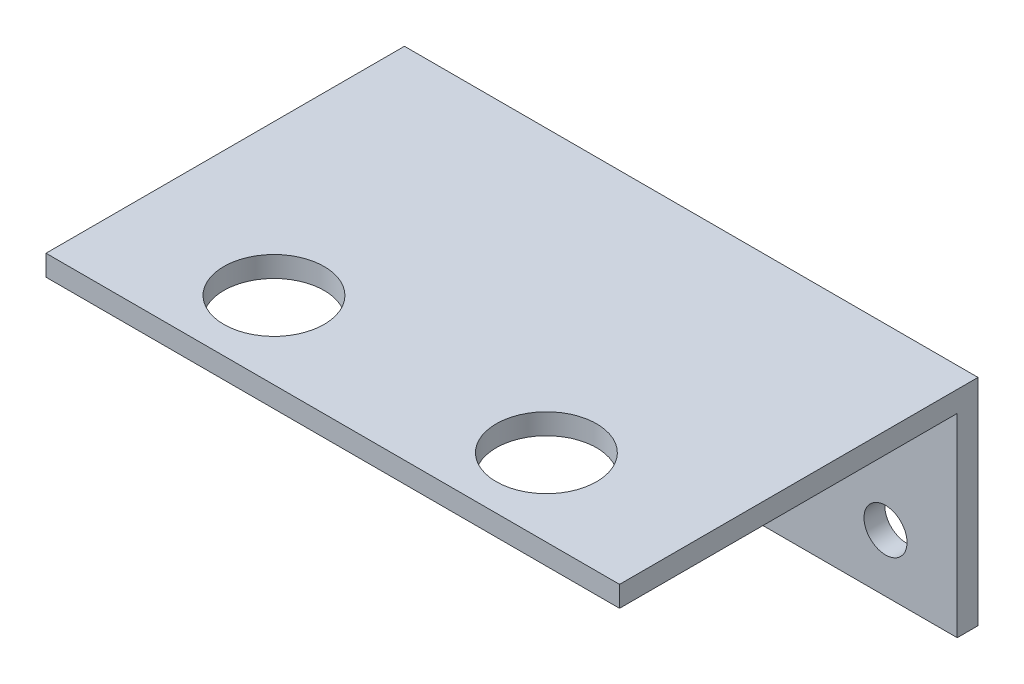
SolidWorks part; units mm, degrees
ref_plane "Front Plane" through (0, 0, 0) normal (0, 0, 1) x (1, 0, 0)
ref_plane "Top Plane" through (0, 0, 0) normal (0, 1, 0) x (1, 0, 0)
ref_plane "Right Plane" through (0, 0, 0) normal (1, 0, 0) x (0, 0, -1)
sketch "Sketch1" plane through (0, 0, 0) normal (0, 0, 1) x (1, 0, 0)
  line L1 (-20, -7.5) -> (20, -7.5)
  line L2 (-20, -7.5) -> (-20, 7.5)
  line L3 (-20, 7.5) -> (20, 7.5)
  line L4 (20, -7.5) -> (20, 7.5)
  line L5 (-20, -7.5) -> (20, 7.5) construction
  line L6 (-20, 7.5) -> (20, -7.5) construction
  point P0 (0, 0)
  dimension "D1" = 15
  dimension "D2" = 40
extrude "Boss-Extrude1" add sketch "Sketch1" along normal blind 1.45
sketch "Sketch2" plane through (0, 0, 1.45) normal (0, 0, 1) x (1, 0, 0)
  line L0 (20, -7.5) -> (20, 7.5) construction
  line L1 (-20, 7.5) -> (20, 7.5)
  line L2 (-20, 7.5) -> (-20, 6.05)
  line L3 (-20, 6.05) -> (20, 6.05)
  line L4 (20, 7.5) -> (20, 6.05)
  dimension "D1" = 1.45
extrude "Boss-Extrude2" add sketch "Sketch2" along normal blind 23.55
sketch "Sketch3" plane through (0, 0, 1.45) normal (0, 0, 1) x (1, 0, 0)
  line L0 (-20, 6.05) -> (-20, -7.5) construction
  line L1 (-20, -7.5) -> (20, -7.5) construction
  circle A0 centre (-15, -3.5) radius 1.5
  dimension "D1" = 3
  dimension "D2" = 5
  dimension "D3" = 4
extrude "Cut-Extrude1" cut sketch "Sketch3" against normal up to next (1.45 mm away)
mirror "Mirror1" about plane through (0, 0, 0) normal (1, 0, 0) of "Cut-Extrude1"
sketch "Sketch4" plane through (0, 7.5, 0) normal (0, 1, 0) x (1, 0, 0)
  line L0 (20, -25) -> (-20, -25) construction
  line L1 (-20, -25) -> (-20, 0) construction
  circle A0 centre (-9.5, -19.6) radius 3.5
  dimension "D1" = 7
  dimension "D2" = 5.4
  dimension "D3" = 10.5
extrude "Cut-Extrude2" cut sketch "Sketch4" against normal up to next (1.45 mm away)
mirror "Mirror2" about plane through (0, 0, 0) normal (1, 0, 0) of "Cut-Extrude2"
